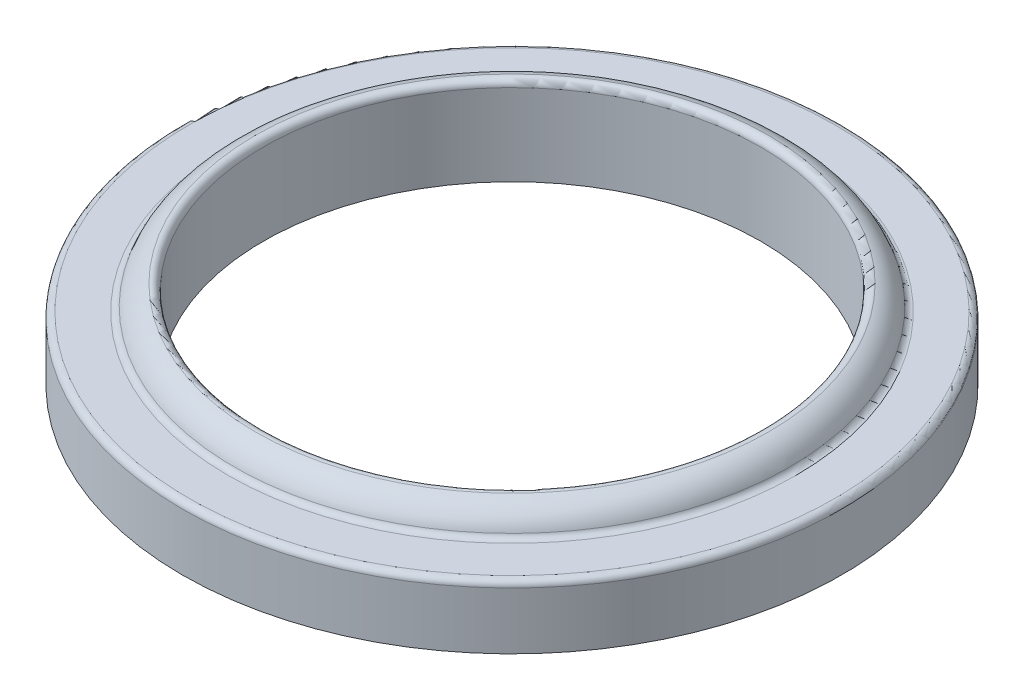
SolidWorks part; units mm, degrees
ref_plane "Front Plane" through (0, 0, 0) normal (0, 0, 1) x (1, 0, 0)
ref_plane "Top Plane" through (0, 0, 0) normal (0, 1, 0) x (1, 0, 0)
ref_plane "Right Plane" through (0, 0, 0) normal (1, 0, 0) x (0, 0, -1)
sketch "Sketch1" plane through (0, 0, 0) normal (0, 0, 1) x (1, 0, 0)
  line L0 (0, 0) -> (0, 27.861) construction
  line L1 (-9.9695, 0) -> (-9.9695, 3.556)
  line L2 (-11.176, 2.54) -> (-13.208, 2.54)
  line L3 (-13.208, 2.54) -> (-13.208, 0)
  line L4 (-13.208, 0) -> (-9.9695, 0)
  arc A0 (-9.9695, 3.556) -> (-11.176, 2.54) centre (-9.9695, 2.3316) ccw
  dimension "D1" = 26.416
  dimension "D2" = 19.939
  dimension "D3" = 2.54
  dimension "D4" = 2.032
  dimension "D5" = 3.556
revolve "Revolve1" add sketch "Sketch1" angle 360 about L0
fillet "Fillet1" radius 0.254 3 edges at (0, 3.556, -9.9695) (0, 2.54, -13.208) (0, 2.54, -11.176)
